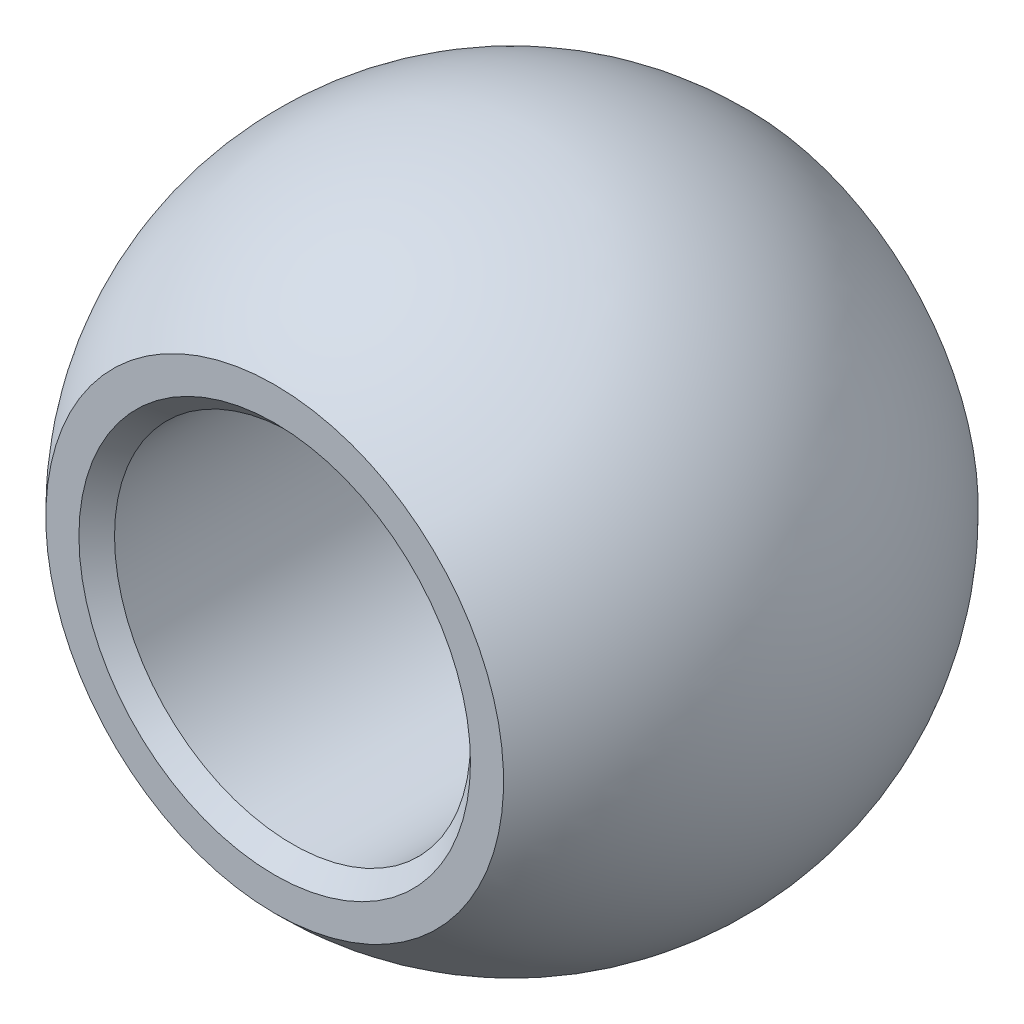
SolidWorks part; units mm, degrees
ref_plane "Front" through (0, 0, 0) normal (0, 0, 1) x (1, 0, 0)
ref_plane "Top" through (0, 0, 0) normal (0, 1, 0) x (1, 0, 0)
ref_plane "Right" through (0, 0, 0) normal (1, 0, 0) x (0, 0, -1)
sketch "Sketch7" plane through (0, 0, 0) normal (0, 0, 1) x (1, 0, 0)
  line L0 (0, 11.115) -> (0, -11.115)
  line L3 (0, 0) -> (11.115, 0) construction
  arc A0 (0, -11.115) -> (0, 11.115) centre (0, 0) ccw
  dimension "D1" = 11.115
  dimension "D2" = 22.23
revolve "Revolve3" add sketch "Sketch7" angle 360 about L0
sketch "Sketch8" plane through (0, 0, 0) normal (1, 0, 0) x (0, 0, -1)
  line L0 (-8, 18) -> (8, -18) construction
  line L1 (-8, 18) -> (8, 18) construction
  line L2 (-8, 18) -> (-8, -18)
  line L3 (-8, -18) -> (8, -18) construction
  line L4 (8, 18) -> (8, -18)
  line L5 (8, 18) -> (15, 18)
  line L6 (15, 18) -> (15, -18)
  line L7 (15, -18) -> (8, -18)
  line L8 (-8, -18) -> (-15, -18)
  line L9 (-15, -18) -> (-15, 18)
  line L10 (-15, 18) -> (-8, 18)
  dimension "D1" = 36
  dimension "D2" = 7
  dimension "D3" = 16
  dimension "D4" = 7
extrude "Cut-Extrude3" cut sketch "Sketch8" against normal through all and the other way through all
sketch "Sketch10" plane through (0, 0, 0) normal (0, 0, 1) x (1, 0, 0)
  circle A1 centre (0, 0) radius 6
  dimension "D1" = 12
extrude "Cut-Extrude4" cut sketch "Sketch10" against normal through all and the other way through all
chamfer "Chamfer1" distance 0.6 angle 45 2 edges at (6, 0, -8) (6, 0, 8)
sketch "Sketch11" plane through (0, 0, 0) normal (1, 0, 0) x (0, 0, -1)
  line L0 (0, 0) -> (-8, 1.9206) construction
  line L2 (0, 0) -> (-8, -1.9206) construction
  line L4 (-8, 18) -> (-8, -18) construction
  line L5 (0, 0) -> (0.0074, 0) construction
  dimension "Swivel" = 27
